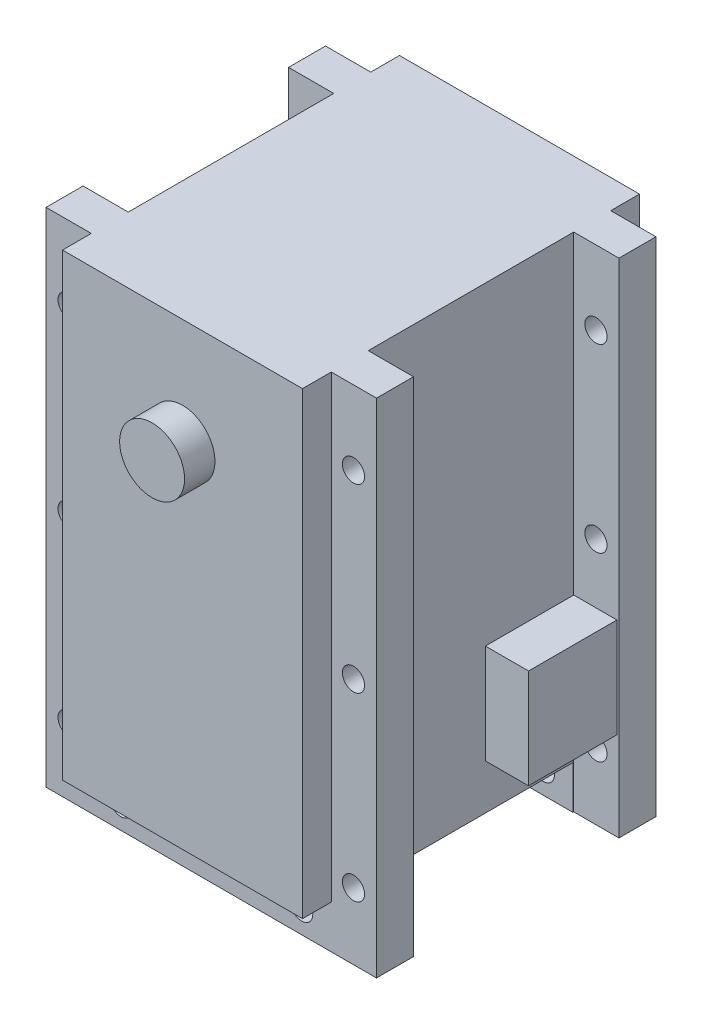
SolidWorks part; units mm, degrees
ref_plane "정면" through (0, 0, 0) normal (0, 0, 1) x (1, 0, 0)
ref_plane "윗면" through (0, 0, 0) normal (0, 1, 0) x (1, 0, 0)
ref_plane "우측면" through (0, 0, 0) normal (1, 0, 0) x (0, 0, -1)
sketch "스케치2" plane through (0, 0, 0) normal (0, 0, 1) x (1, 0, 0)
  line L1 (0, 0) -> (40.2, 0)
  line L2 (0, 0) -> (0, 61.1)
  line L3 (0, 61.1) -> (40.2, 61.1)
  line L4 (40.2, 0) -> (40.2, 61.1)
  dimension "D1" = 61.1
  dimension "D2" = 40.2
extrude "보스-돌출1" add sketch "스케치2" along normal mid plane 41
ref_plane "평면5" through (40.2, 0, 20.5) normal (0, 1, 0) x (1, 0, 0)
sketch "스케치9" plane through (40.2, 0, 0) normal (1, 0, 0) x (0, 0, -1)
  line L0 (-20.5, 0) -> (-20.5, 61.1) construction
  line L1 (-20.5, 5.25) -> (-17, 5.25)
  line L2 (-20.5, 5.25) -> (-20.5, 0)
  line L3 (-20.5, 0) -> (-17, 0)
  line L4 (20.5, 5.25) -> (20.5, 0)
  line L5 (-12.4, 5.25) -> (12.4, 5.25)
  line L6 (-12.4, 5.25) -> (12.4, 5.25)
  line L7 (-17, 5.25) -> (-17, 0)
  line L8 (-12.4, 0) -> (12.4, 0)
  line L9 (17, 5.25) -> (17, 0)
  line L10 (-12.4, 5.25) -> (12.4, 5.25)
  line L11 (-12.4, 5.25) -> (-12.4, 0)
  line L12 (-12.4, 0) -> (12.4, 0)
  line L13 (12.4, 5.25) -> (12.4, 0)
  line L14 (17, 5.25) -> (20.5, 5.25)
  line L15 (17, 0) -> (20.5, 0)
  line L16 (-12.4, 0) -> (12.4, 0)
  line M9 (20.5, 0) -> (20.5, 61.1)
  line M11 (-20.5, 61.1) -> (-20.5, 0)
  line M12 (-20.5, 0) -> (20.5, 0)
  dimension "D1" = 5.25
  dimension "D2" = 3.5
  dimension "D3" = 3.5
  dimension "D4" = 4.6
  dimension "D5" = 4.6
extrude "컷-돌출3" cut sketch "스케치9" against normal through all contours L13 L5 L11 M12 | L7 L1 M11 M12 | L14 L9 M12 M9
sketch "스케치10" plane through (0, 61.1, 0) normal (0, 1, 0) x (1, 0, 0)
  line L0 (40.2, -20.5) -> (0, -20.5) construction
  line L1 (5.5, -20.5) -> (0, -20.5)
  line L2 (5.5, -20.5) -> (5.5, -17)
  line L3 (5.5, 20.5) -> (0, 20.5)
  line L4 (0, -20.5) -> (0, -17)
  line L5 (5.5, -12.5) -> (5.5, 12.5)
  line L6 (34.7, -20.5) -> (40.2, -20.5)
  line L7 (34.7, -20.5) -> (34.7, -17)
  line L8 (34.7, 20.5) -> (40.2, 20.5)
  line L9 (40.2, -20.5) -> (40.2, -17)
  line L10 (0, 17) -> (5.5, 17)
  line L11 (0, 12.5) -> (0, -12.5)
  line L12 (0, -17) -> (5.5, -17)
  line L13 (5.5, 12.5) -> (5.5, -12.5)
  line L14 (34.7, -17) -> (40.2, -17)
  line L15 (34.7, -12.5) -> (34.7, 12.5)
  line L16 (34.7, 17) -> (40.2, 17)
  line L17 (40.2, -12.5) -> (40.2, 12.5)
  line L18 (0, -12.5) -> (5.5, -12.5)
  line L19 (0, -12.5) -> (0, 12.5)
  line L20 (0, 12.5) -> (5.5, 12.5)
  line L21 (5.5, -12.5) -> (5.5, 12.5)
  line L22 (34.7, -12.5) -> (40.2, -12.5)
  line L23 (34.7, -12.5) -> (34.7, 12.5)
  line L24 (34.7, 12.5) -> (40.2, 12.5)
  line L25 (40.2, -12.5) -> (40.2, 12.5)
  line L26 (0, -12.5) -> (0, 12.5)
  line L27 (5.5, 17) -> (5.5, 20.5)
  line L28 (0, 17) -> (0, 20.5)
  line L29 (34.7, 17) -> (34.7, 20.5)
  line L30 (40.2, 17) -> (40.2, 20.5)
  line L31 (34.7, -12.5) -> (34.7, 12.5)
  line L32 (40.2, -12.5) -> (40.2, 12.5)
  line M15 (40.2, 20.5) -> (0, 20.5)
  line M16 (0, 20.5) -> (0, -20.5)
  line M18 (40.2, -20.5) -> (40.2, 20.5)
  dimension "D1" = 5.5
  dimension "D2" = 5.5
  dimension "D3" = 3.5
  dimension "D4" = 3.5
  dimension "D5" = 3.5
  dimension "D6" = 3.5
  dimension "D7" = 4.5
  dimension "D8" = 4.5
  dimension "D9" = 4.5
  dimension "D10" = 4.5
extrude "컷-돌출4" cut sketch "스케치10" against normal through all contours L20 L18 L5 M16 | L10 L27 M15 M16 | L24 L15 L22 M18 | L29 L16 M18 M15 | L12 L2 L1 L4 | L14 L9 L6 L7
sketch "스케치12" plane through (0, 0, 20.5) normal (0, 0, 1) x (1, 0, 0)
  line L3 (0, 61.1) -> (0, 0) construction
  line L4 (95.2, 0) -> (-14.8, 0) construction
  line L5 (0, 61.1) -> (5.5, 61.1) construction
  circle A1 centre (9.1, 2.8) radius 1.35
  circle A2 centre (31.1, 2.8) radius 1.35
  circle A3 centre (2.8, 52.1) radius 1.35
  circle A4 centre (37.4, 52.1) radius 1.35
  circle A5 centre (2.8, 30.1) radius 1.35
  circle A6 centre (37.4, 30.1) radius 1.35
  circle A7 centre (2.8, 8.1) radius 1.35
  circle A8 centre (37.4, 8.1) radius 1.35
  point P22 (0, 0)
  point P23 (0, 0)
  point P24 (0, 0)
  dimension "D1" = 22
  dimension "D3" = 2.7
  dimension "D4" = 2.7
  dimension "D8" = 2.7
  dimension "D9" = 2.7
  dimension "D11" = 2.7
  dimension "D12" = 2.7
  dimension "D14" = 2.7
  dimension "D15" = 2.7
  dimension "D2" = 9.1
  dimension "D5" = 2.8
  dimension "D6" = 34.6
  dimension "D7" = 2.8
  dimension "D10" = 9
  dimension "D13" = 22
  dimension "D16" = 22
extrude "컷-돌출5" cut sketch "스케치12" against normal through all contours A3 | A5 | A7 | A8 | A6 | A4 | A2 | A1
sketch "스케치13" plane through (0, 0, 20.5) normal (0, 0, 1) x (1, 0, 0)
  line L0 (34.7, 61.1) -> (5.5, 61.1) construction
  line L1 (40.2, 61.1) -> (40.2, 0) construction
  circle A0 centre (20.1, 48.1) radius 3.95
  dimension "D1" = 7.9
  dimension "D2" = 13
  dimension "D3" = 20.1
extrude "보스-돌출2" add sketch "스케치13" along normal blind 3.7 contours A0
sketch "스케치14" plane through (0, 0, -20.5) normal (0, 0, -1) x (-1, 0, 0)
  line L0 (-34.7, 61.1) -> (-5.5, 61.1) construction
  line L1 (0, 61.1) -> (0, 0) construction
  circle A0 centre (-20.1, 48.1) radius 3.95
  dimension "D1" = 7.9
  dimension "D2" = 13
  dimension "D3" = 20.1
extrude "보스-돌출4" add sketch "스케치14" along normal blind 1
sketch "스케치16" plane through (34.7, 0, 0) normal (1, 0, 0) x (0, 0, -1)
  line L0 (12.5, 0) -> (12.5, 61.1) construction
  line L1 (12.5, 10.75) -> (1.75, 10.75)
  line L6 (12.5, 0) -> (12.5, 61.1) construction
  line L7 (1.75, 10.75) -> (12.5, 10.75)
  line L8 (1.75, 10.75) -> (1.75, 22.85)
  line L9 (1.75, 22.85) -> (12.5, 22.85)
  line L10 (12.5, 10.75) -> (12.5, 22.85)
  line M5 (12.5, 0) -> (12.5, 61.1)
  dimension "D1" = 10.75
  dimension "D3" = 12.1
extrude "보스-돌출6" add sketch "스케치16" along normal blind 5.25 and the other way blind 34.25 contours L9 L8 L1 M5
